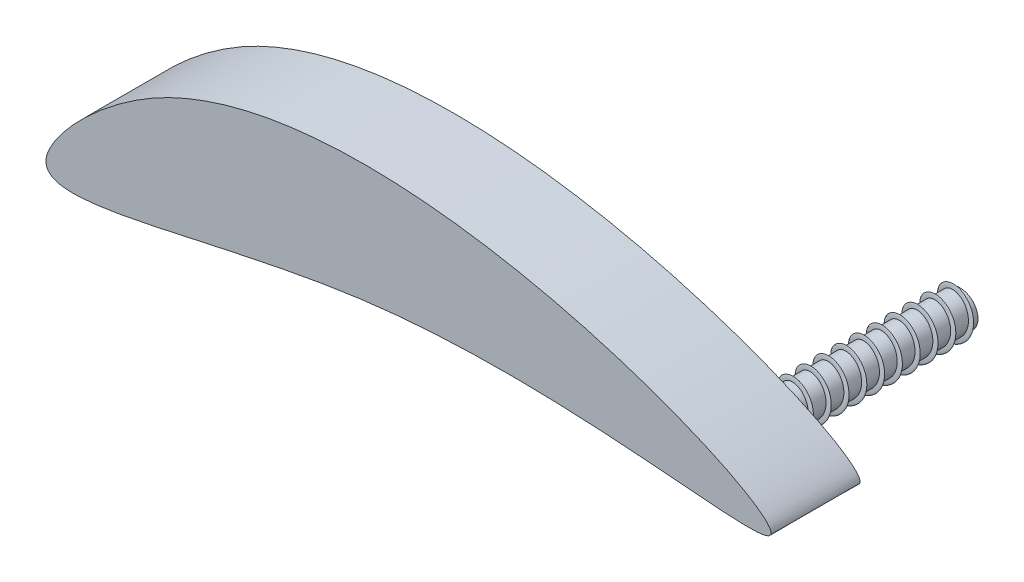
SolidWorks part; units mm, degrees
ref_plane "Front Plane" through (0, 0, 0) normal (0, 0, 1) x (1, 0, 0)
ref_plane "Top Plane" through (0, 0, 0) normal (0, 1, 0) x (1, 0, 0)
ref_plane "Right Plane" through (0, 0, 0) normal (1, 0, 0) x (0, 0, -1)
sketch "Sketch1" plane through (0, 0, 0) normal (0, 0, 1) x (1, 0, 0)
  spline S0 degree 3 poles (20.9319, 5.2826) (-5.1658, -4.5396) (13.567, 15.4467) (56.4101, -2.8915) (20.9319, 5.2826) (-5.1658, -4.5396) (13.567, 15.4467) knots -0.900565 -0.485275 -0.214138 0 0.099435 0.514725 0.785862 1 1.099435 1.514725 1.785862 only from (0, 0) to (0, 0)
extrude "Boss-Extrude1" add sketch "Sketch1" against normal blind 5
sketch "Sketch6" plane through (0, 0, -5) normal (0, 0, -1) x (-1, 0, 0)
  circle A0 centre (-36.3302, 3.2342) radius 1
  point P2 (-36.3302, 3.2342)
extrude "Boss-Extrude2" add sketch "Sketch6" along normal blind 10
ref_plane "Plane1" through (0, 0, -5) normal (0, 0, -1) x (-1, 0, 0)
sketch "Sketch7" plane through (0, 0, -5) normal (0, 0, -1) x (-1, 0, 0)
  circle A0 centre (-36.3302, 3.2342) radius 1
curve "Helix/Spiral1" pitch 1 height 10 turns 10
sketch "Sketch8" plane through (0, 0, -5) normal (0, 0, -1) x (-1, 0, 0)
  circle A0 centre (-35.3325, 3.1669) radius 0.25
  circle A1 centre (-36.3302, 3.2342) radius 1 construction
sweep "Sweep1" add profiles "Sketch8" path "Helix/Spiral1"
